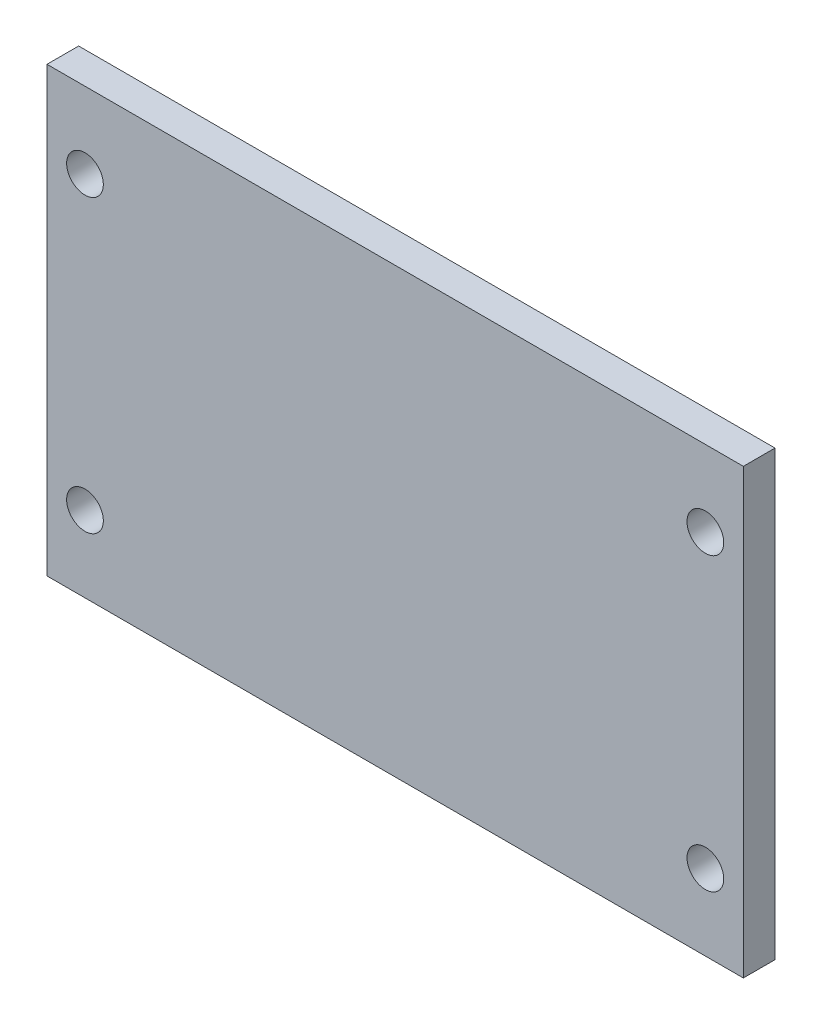
SolidWorks part; units mm, degrees
material "1.0545 (S355N)"
ref_plane "Front Plane" through (0, 0, 0) normal (0, 0, 1) x (1, 0, 0)
ref_plane "Top Plane" through (0, 0, 0) normal (0, 1, 0) x (1, 0, 0)
ref_plane "Right Plane" through (0, 0, 0) normal (1, 0, 0) x (0, 0, -1)
sketch "Sketch1" plane through (0, 0, 0) normal (0, 0, 1) x (1, 0, 0)
  line L0 (0, 0) -> (0, 106.3954) construction
  line L1 (-55, 35) -> (55, 35)
  line L2 (-55, 35) -> (-55, -35)
  line L3 (-55, -35) -> (55, -35)
  line L4 (55, 35) -> (55, -35)
  line L5 (-100.1633, 0) -> (116.2332, 0) construction
  dimension "D1" = 110
  dimension "D2" = 70
  dimension "D3" = 35
extrude "Boss-Extrude1" add sketch "Sketch1" along normal mid plane 5
sketch "Sketch3" plane through (0, 0, 2.5) normal (0, 0, 1) x (1, 0, 0)
  line L0 (-67.2676, 0) -> (78.5686, 0) construction
  line L1 (0, 38.208) -> (0, -42.6208) construction
  point P0 (-49, 23)
  point P1 (-49, -23)
  point P2 (49, -23)
  point P3 (49, 23)
  dimension "D1" = 98
  dimension "D2" = 46
hole_wizard "M5 Clearance Hole1" positions "Sketch6" profile "Sketch8" hole size "M5" standard "ISO" end condition through all
sketch "Sketch6" plane through (0, 0, 2.5) normal (0, 0, 1) x (1, 0, 0)
  point P0 (-49, 23)
  point P3 (-49, -23)
  point P6 (49, -23)
  point P9 (49, 23)
sketch "Sketch8" plane through (-49, 23, 2.5) normal (1, 0, 0) x (0, -1, 0)
  line L0 (0, 0) -> (0, 5)
  line L1 (0, 5) -> (2.9, 5)
  line L2 (2.9, 5) -> (2.9, 0)
  line L5 (2.9, 0) -> (0, 0)
  line L11 (0, -6.35) -> (0, 107.95) construction
  dimension "Thru Hole Dia." = 5.8
  dimension "Thru Hole Depth" = 5
